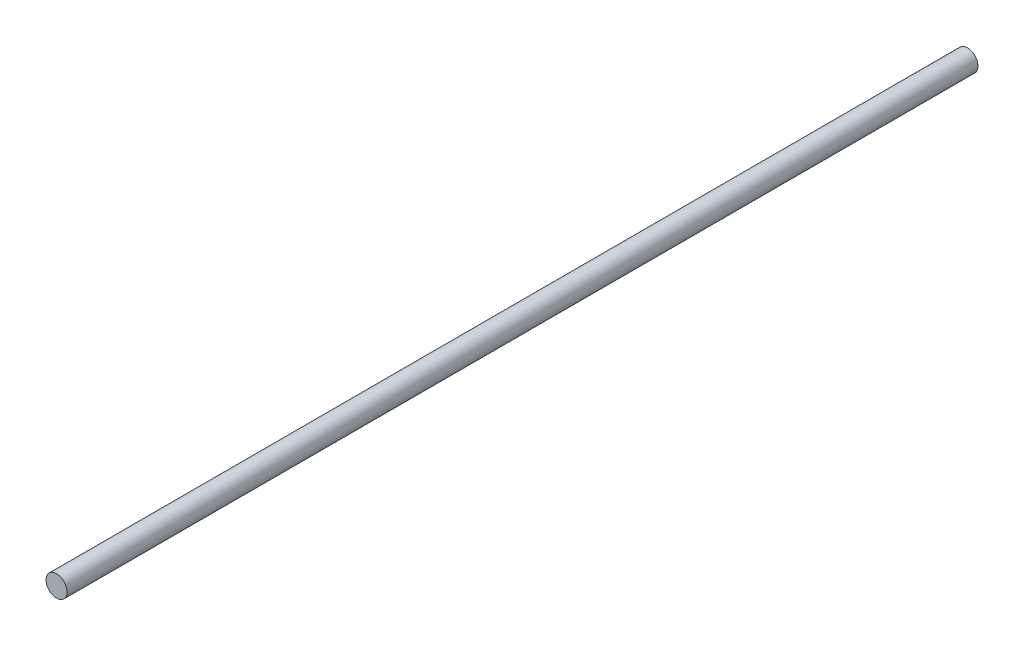
SolidWorks part; units mm, degrees
ref_plane "前视基准面" through (0, 0, 0) normal (0, 0, 1) x (1, 0, 0)
ref_plane "上视基准面" through (0, 0, 0) normal (0, 1, 0) x (1, 0, 0)
ref_plane "右视基准面" through (0, 0, 0) normal (1, 0, 0) x (0, 0, -1)
sketch "草图1" plane through (0, 0, 0) normal (0, 0, 1) x (1, 0, 0)
  circle A0 centre (0, 0) radius 2.9
  dimension "D1" = 5.8
extrude "凸台-拉伸1" add sketch "草图1" along normal blind 250
